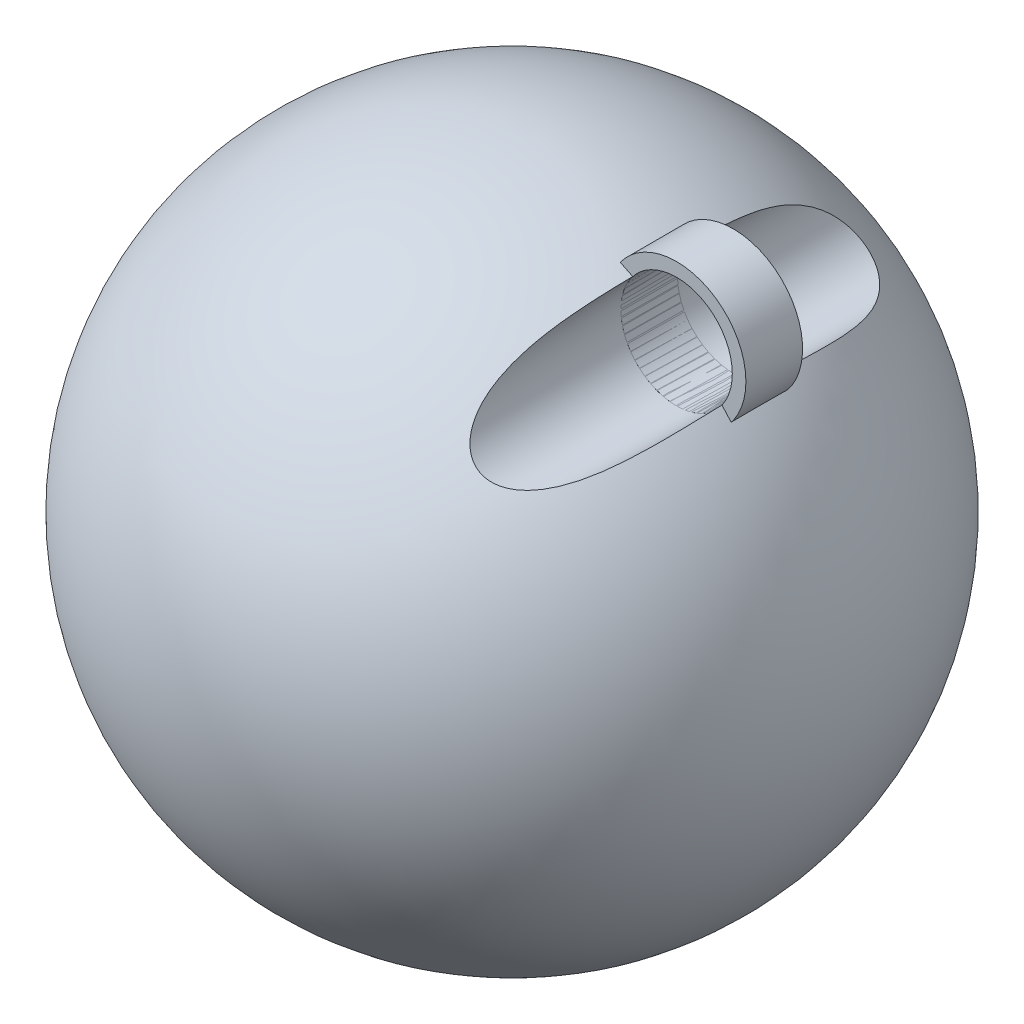
SolidWorks part; units mm, degrees
ref_plane "Ebene vorne" through (0, 0, 0) normal (0, 0, 1) x (1, 0, 0)
ref_plane "Ebene oben" through (0, 0, 0) normal (0, 1, 0) x (1, 0, 0)
ref_plane "Ebene rechts" through (0, 0, 0) normal (1, 0, 0) x (0, 0, -1)
sketch "Skizze1" plane through (0, 0, 0) normal (0, 0, 1) x (1, 0, 0)
  line L0 (0, -100.0577) -> (0, -681.5251)
  arc A0 (0, -681.5251) -> (0, -100.0577) centre (0, -390.7914) ccw
revolve "Rotation1" add sketch "Skizze1" angle 360 about L0
sketch "Skizze2" plane through (0, 0, 0) normal (0, 0, 1) x (1, 0, 0)
  arc A0 (121.127, -126.4917) -> (219.1017, -199.6879) centre (170.1143, -163.0898) cw
  arc A1 (0, -681.5251) -> (0, -100.0577) centre (0, -390.7914) ccw construction
  arc A2 (121.127, -126.4917) -> (219.1017, -199.6879) centre (170.1143, -163.0898) ccw
  arc A3 (130.7404, -133.6738) -> (209.4883, -192.5058) centre (170.1143, -163.0898) cw
  arc A4 (130.7404, -133.6738) -> (209.4883, -192.5058) centre (170.1143, -163.0898) ccw
  point P3 (170.1143, -163.0898)
  point P7 (130.7404, -133.6738)
  point P8 (209.4883, -192.5058)
  dimension "D1" = 12
extrude "Aufsatz-Linear austragen1" add sketch "Skizze2" along normal mid plane 50 separate body
sketch "Skizze5" plane through (0, 0, 0) normal (0, 0, 1) x (1, 0, 0)
  circle A0 centre (170.1143, -163.0898) radius 49.1488 construction
  circle A1 centre (170.1143, -163.0898) radius 49.1488
extrude "Schnitt-Linear austragen3" cut sketch "Skizze5" against normal mid plane 400
sketch "Skizze7" plane through (0, 0, 0) normal (0, 0, 1) x (1, 0, 0)
  line L0 (0, -100.0577) -> (0, -681.5251) construction
  spline S0 degree 3 poles (34.6425, -207.416) (-11.5478, -254.0653) (-23.0708, -330.4015) (-5.5228, -370.9994) (-4.576, -372.9367) knots 0 0 0 0 0.95 1 1 1 1
  spline S1 degree 3 poles (-4.576, -372.9367) (-3.6383, -375.0626) (17.0691, -416.3994) (78.1848, -442.6053) (83.6368, -495.1637) knots 0 0 0 0 0.05 1 1 1 1
  spline S2 degree 3 poles (83.6368, -495.1637) (88.3874, -540.9613) (62.3894, -575.8986) (0, -584.0435) knots 0 0 0 0 1 1 1 1
  spline S3 degree 1 poles (0, -584.0435) (0, -583.5519) knots 0 0 1 1
  spline S4 degree 3 poles (0, -584.0435) (-47.4723, -590.241) (-108.0579, -562.5295) (-110.8832, -514.0834) knots 0 0 0 0 1 1 1 1
  spline S5 degree 2 poles (-67.0201, -450.3828) (-114.0792, -459.2811) (-110.8832, -514.0834) knots 0 0 0 1 1 1
  spline S6 degree 3 poles (-67.0201, -450.3828) (-111.4569, -472.2308) (-104.673, -537.2161) (-49.8375, -551.7009) knots 0 0 0 0 1 1 1 1
  spline S7 degree 3 poles (-49.8375, -551.7009) (-1.6695, -564.4246) (50.6862, -541.5077) (49.4069, -506.9669) knots 0 0 0 0 1 1 1 1
  spline S8 degree 3 poles (49.4069, -506.9669) (48.6045, -485.3026) (39.3371, -469.7277) (0, -430.9608) knots 0 0 0 0 1 1 1 1
  spline S9 degree 3 poles (0, -430.9608) (-23.9586, -407.3494) (-41.7912, -370.1177) (-37.9337, -332.8289) knots 0 0 0 0 1 1 1 1
  spline S10 degree 3 poles (34.6425, -207.416) (-9.8794, -238.6351) (-32.6584, -281.8344) (-37.9337, -332.8289) knots 0 0 0 0 1 1 1 1
